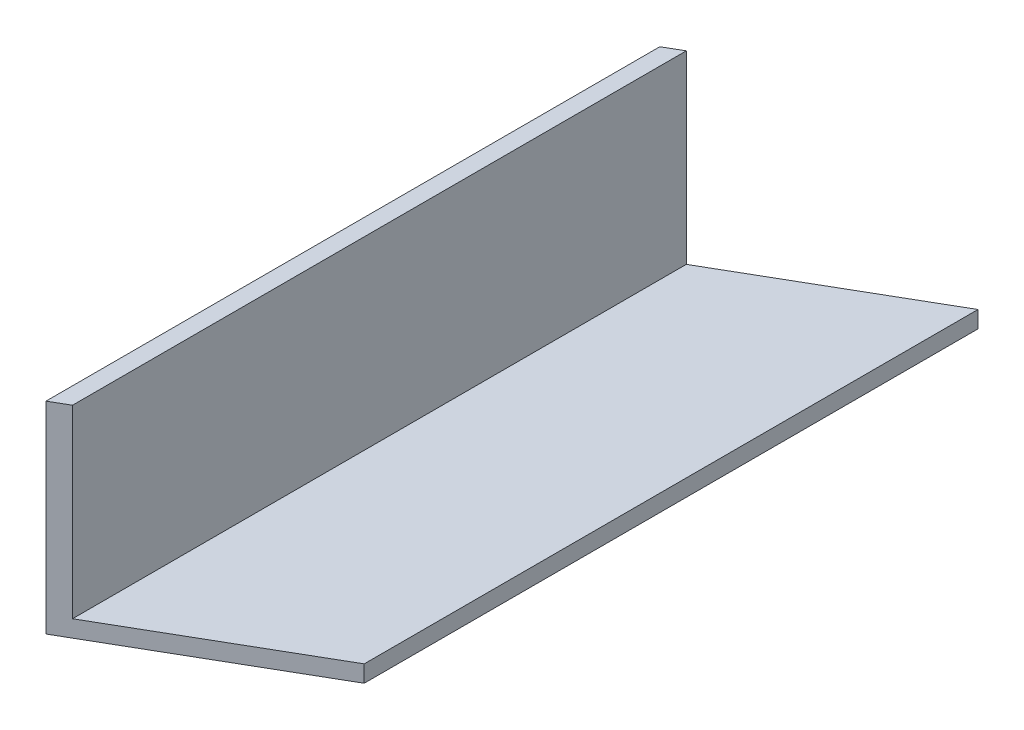
SolidWorks part; units mm, degrees
ref_plane "Front Plane" through (0, 0, 0) normal (0, 0, 1) x (1, 0, 0)
ref_plane "Top Plane" through (0, 0, 0) normal (0, 1, 0) x (1, 0, 0)
ref_plane "Right Plane" through (0, 0, 0) normal (1, 0, 0) x (0, 0, -1)
sketch "Sketch1" plane through (0, 0, 0) normal (0, 0, 1) x (1, 0, 0)
  line L1 (0, 0) -> (38.1, 0)
  line L2 (0, 0) -> (0, 38.1)
  line L3 (0, 38.1) -> (38.1, 38.1)
  line L4 (38.1, 0) -> (38.1, 38.1)
extrude "Boss-Extrude1" add sketch "Sketch1" along normal blind 137.922
sketch "Sketch2" plane through (0, 0, 137.922) normal (0, 0, 1) x (1, 0, 0)
  line L1 (38.1, 38.1) -> (3.175, 38.1)
  line L2 (38.1, 38.1) -> (38.1, 3.175)
  line L3 (38.1, 3.175) -> (3.175, 3.175)
  line L4 (3.175, 38.1) -> (3.175, 3.175)
extrude "Cut-Extrude1" cut sketch "Sketch2" against normal through all
sketch "Sketch3" plane through (0, 0, 0) normal (0, -1, 0) x (1, 0, 0)
  line L0 (0, 137.922) -> (38.1, 137.922)
  line L1 (38.1, 137.922) -> (38.1, 115.925)
  line L2 (38.1, 137.922) -> (38.1, 0) construction
  line L3 (38.1, 115.925) -> (0, 137.922)
  line L4 (38.1, 0) -> (0, 0)
  line L5 (0, 0) -> (0, 21.997)
  line L6 (0, 137.922) -> (0, 0) construction
  line L7 (0, 21.997) -> (38.1, 0)
  dimension "D1" = 60
  dimension "D2" = 60
extrude "Cut-Extrude2" cut sketch "Sketch3" against normal through all
